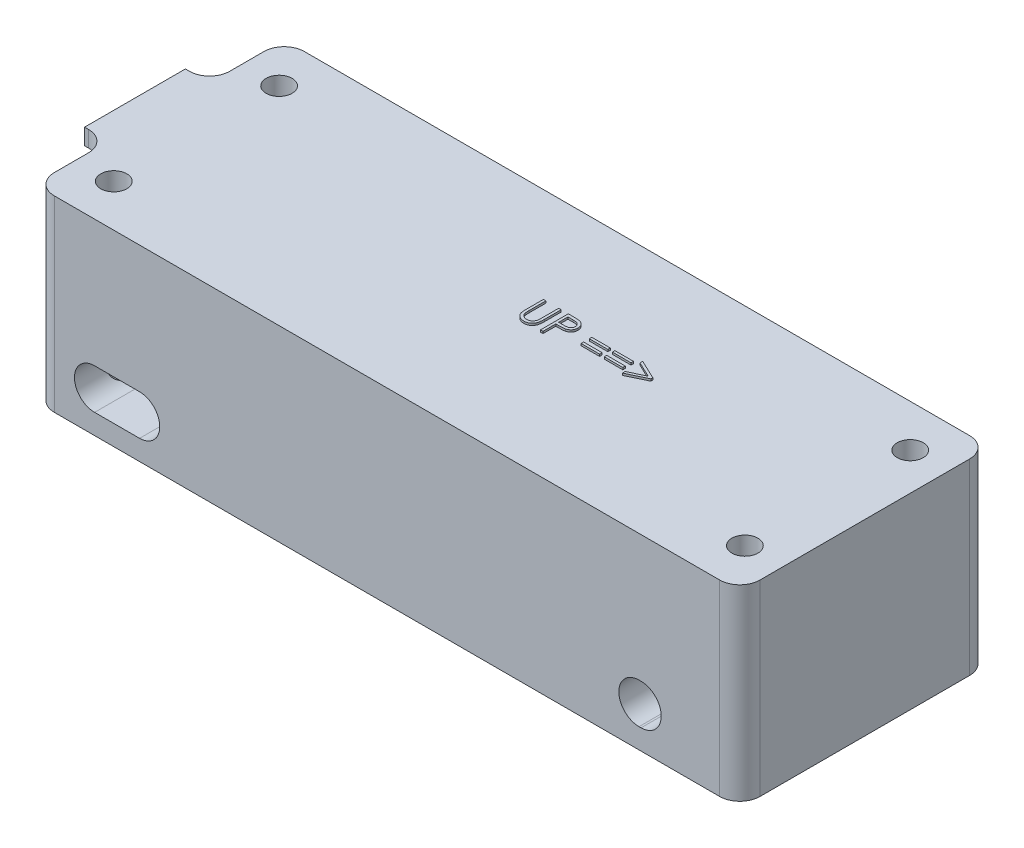
SolidWorks part; units mm, degrees
ref_plane "Front Plane" through (0, 0, 0) normal (0, 0, 1) x (1, 0, 0)
ref_plane "Top Plane" through (0, 0, 0) normal (0, 1, 0) x (1, 0, 0)
ref_plane "Right Plane" through (0, 0, 0) normal (1, 0, 0) x (0, 0, -1)
sketch "Sketch1" plane through (0, 0, 0) normal (0, 1, 0) x (1, 0, 0)
  line L1 (-41.91, 15.748) -> (41.91, 15.748)
  line L2 (-44.45, 13.208) -> (-44.45, -13.208)
  line L3 (-41.91, -15.748) -> (41.91, -15.748)
  line L4 (44.45, 13.208) -> (44.45, -13.208)
  line L5 (-44.45, 15.748) -> (44.45, -15.748) construction
  line L6 (-44.45, -15.748) -> (44.45, 15.748) construction
  arc A1 (-44.45, -13.208) -> (-41.91, -15.748) centre (-41.91, -13.208) ccw
  arc A2 (41.91, -15.748) -> (44.45, -13.208) centre (41.91, -13.208) ccw
  arc A3 (41.91, 15.748) -> (44.45, 13.208) centre (41.91, 13.208) cw
  arc A4 (-41.91, 15.748) -> (-44.45, 13.208) centre (-41.91, 13.208) ccw
  point P0 (0, 0)
  dimension "D3" = 2.54
  dimension "D1" = 31.496
  dimension "D2" = 88.9
extrude "Boss-Extrude1" add sketch "Sketch1" along normal blind 21.59
sketch "Sketch2" plane through (0, 21.59, 0) normal (0, 1, 0) x (1, 0, 0)
  line L0 (-44.45, -8.89) -> (-44.45, -13.208)
  line L1 (-46.99, 6.35) -> (-47.498, 6.35)
  line L3 (-44.45, 0) -> (-47.498, 0) construction
  line L4 (-41.91, -15.748) -> (41.91, -15.748)
  line L5 (44.45, -13.208) -> (44.45, 13.208)
  line L6 (41.91, 15.748) -> (-41.91, 15.748)
  line L7 (-44.45, 13.208) -> (-44.45, -13.208)
  line L8 (-41.91, -15.748) -> (41.91, -15.748)
  line L9 (44.45, -13.208) -> (44.45, 13.208)
  line L10 (41.91, 15.748) -> (-41.91, 15.748)
  line L11 (-44.45, 13.208) -> (-44.45, 8.89)
  line L12 (-47.498, 6.35) -> (-47.498, -6.35)
  line L13 (-46.99, -6.35) -> (-47.498, -6.35)
  arc A0 (-46.99, 6.35) -> (-44.45, 8.89) centre (-46.99, 8.89) ccw
  arc A1 (-46.99, -6.35) -> (-44.45, -8.89) centre (-46.99, -8.89) cw
  arc A4 (-44.45, -13.208) -> (-41.91, -15.748) centre (-41.91, -13.208) ccw
  arc A5 (41.91, -15.748) -> (44.45, -13.208) centre (41.91, -13.208) ccw
  arc A6 (44.45, 13.208) -> (41.91, 15.748) centre (41.91, 13.208) ccw
  arc A7 (-41.91, 15.748) -> (-44.45, 13.208) centre (-41.91, 13.208) ccw
  arc A8 (-44.45, -13.208) -> (-41.91, -15.748) centre (-41.91, -13.208) ccw
  arc A9 (41.91, -15.748) -> (44.45, -13.208) centre (41.91, -13.208) ccw
  arc A10 (44.45, 13.208) -> (41.91, 15.748) centre (41.91, 13.208) ccw
  arc A11 (-41.91, 15.748) -> (-44.45, 13.208) centre (-41.91, 13.208) ccw
  point P15 (0, 0)
  point P19 (-44.45, 6.35)
  dimension "D4" = 2.54
  dimension "D2" = 3.048
  dimension "D3" = 6.35
  dimension "D1" = 0
extrude "Boss-Extrude2" add sketch "Sketch2" along normal blind 2.032
sketch "Sketch3" plane through (0, 23.622, 0) normal (0, 1, 0) x (1, 0, 0)
  text T0 "UP ==>"
extrude "Boss-Extrude3" add sketch "Sketch3" along normal blind 0.254
sketch "Sketch4" plane through (0, 0, 0) normal (0, -1, 0) x (1, 0, 0)
  line L1 (-41.91, 15.748) -> (41.91, 15.748) construction
  line L2 (0, 15.748) -> (0, 8.5055) construction
  line L3 (0, 0) -> (-44.45, 0) construction
  line L4 (-44.45, -13.208) -> (-44.45, 13.208) construction
  circle A0 centre (-39.751, 10.414) radius 1.6383
  circle A1 centre (39.751, 10.414) radius 1.6383
  circle A2 centre (39.751, -10.414) radius 1.6383
  circle A3 centre (-39.751, -10.414) radius 1.6383
  point P13 (0, 0)
  point P14 (0, 0)
  dimension "D1" = 3.2766
  dimension "D2" = 5.334
  dimension "D3" = 79.502
extrude "Cut-Extrude1" cut sketch "Sketch4" against normal blind 27.94
sketch "Sketch6" plane through (0, 0, 15.748) normal (0, 0, 1) x (1, 0, 0)
  line L0 (-41.91, 5.08) -> (41.91, 5.08) construction
  line L1 (-41.91, 23.622) -> (-41.91, 0) construction
  line L2 (41.91, 23.622) -> (41.91, 0) construction
  line L3 (-41.91, 0) -> (41.91, 0) construction
  line L4 (-36.83, 5.08) -> (-31.1658, 5.08) construction
  line L5 (-36.83, 7.62) -> (-31.1658, 7.62)
  line L6 (-36.83, 2.54) -> (-31.1658, 2.54)
  line L7 (-44.45, 23.622) -> (-44.45, 0) construction
  line L8 (31.75, 5.08) -> (32.004, 5.08) construction
  line L9 (31.75, 7.62) -> (32.004, 7.62)
  line L10 (31.75, 2.54) -> (32.004, 2.54)
  line L11 (44.45, 23.622) -> (44.45, 0) construction
  arc A0 (-36.83, 7.62) -> (-36.83, 2.54) centre (-36.83, 5.08) ccw
  arc A1 (-31.1658, 2.54) -> (-31.1658, 7.62) centre (-31.1658, 5.08) ccw
  arc A2 (31.75, 7.62) -> (31.75, 2.54) centre (31.75, 5.08) ccw
  arc A3 (32.004, 2.54) -> (32.004, 7.62) centre (32.004, 5.08) ccw
  point P10 (-33.9979, 5.08)
  point P19 (31.877, 5.08)
  dimension "D3" = 2.54
  dimension "D4" = 7.62
  dimension "D5" = 2.54
  dimension "D1" = 5.08
  dimension "D2" = 5.6642
  dimension "D6" = 0.254
  dimension "D7" = 12.7
extrude "Cut-Extrude2" cut sketch "Sketch6" against normal blind 37.592
